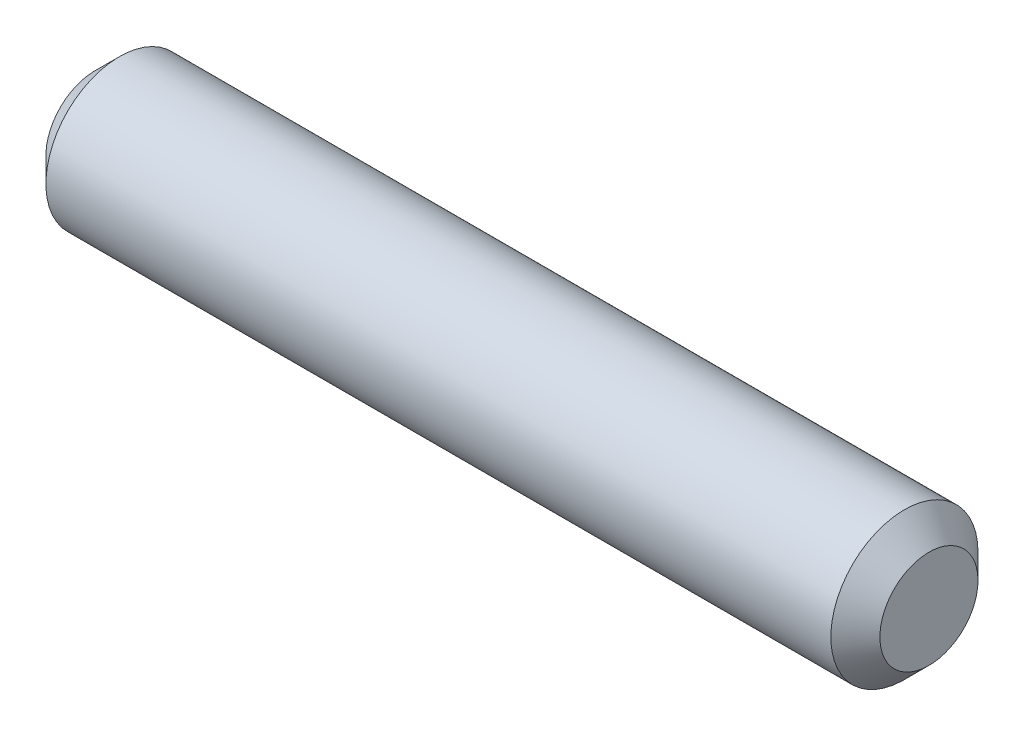
SolidWorks part; units mm, degrees
material "AISI 304"
ref_plane "Plan de face" through (0, 0, 0) normal (0, 0, 1) x (1, 0, 0)
ref_plane "Plan de dessus" through (0, 0, 0) normal (0, 1, 0) x (1, 0, 0)
ref_plane "Plan de droite" through (0, 0, 0) normal (1, 0, 0) x (0, 0, -1)
sketch "Esquisse1" plane through (0, 0, 0) normal (1, 0, 0) x (0, 0, -1)
  circle A0 centre (0, 0) radius 1.5
  dimension "D1" = 3
extrude "AXE" add sketch "Esquisse1" along normal mid plane 17
chamfer "Chanfrein1" distance 0.5 angle 45 2 edges at (-8.5, 0, -1.5) (8.5, 0, -1.5)
